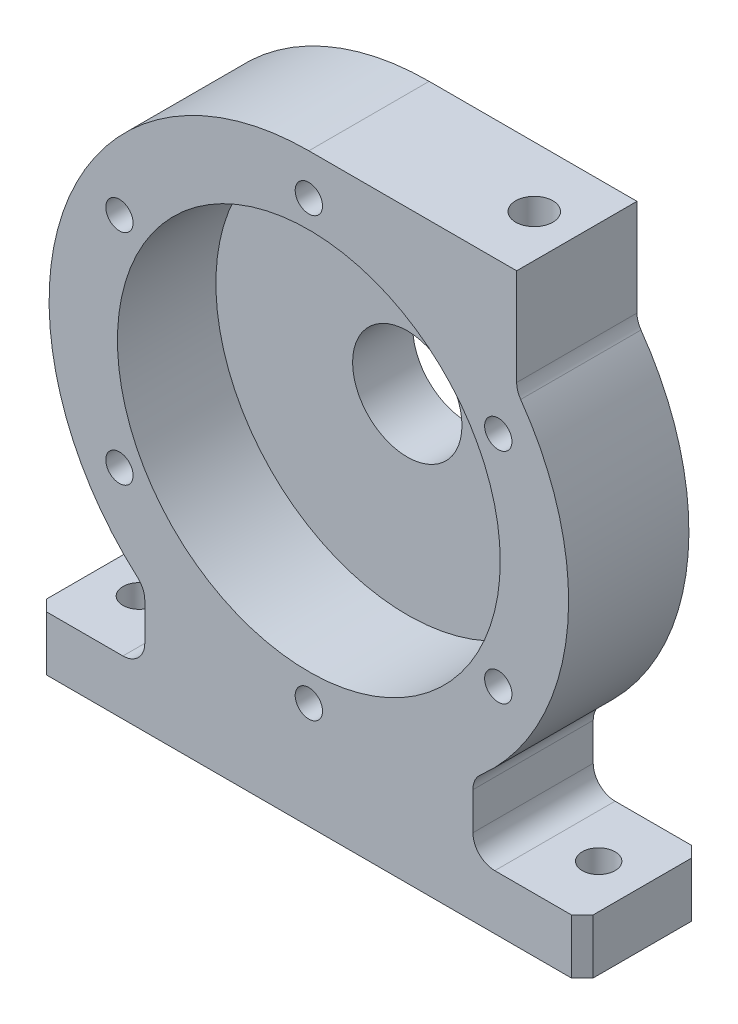
SolidWorks part; units mm, degrees
ref_plane "Front Plane" through (0, 0, 0) normal (0, 0, 1) x (1, 0, 0)
ref_plane "Top Plane" through (0, 0, 0) normal (0, 1, 0) x (1, 0, 0)
ref_plane "Right Plane" through (0, 0, 0) normal (1, 0, 0) x (0, 0, -1)
sketch "Sketch2" plane through (0, 0, 0) normal (0, 0, 1) x (1, 0, 0)
  line L0 (0, 0) -> (0, -59.5) construction
  line L1 (-50, -59.5) -> (50, -59.5)
  line L2 (50, -59.5) -> (50, -49.5)
  line L3 (50, -49.5) -> (34, -49.5)
  line L4 (30, -45.5) -> (30, -38.6814)
  line L5 (0, 47.5) -> (38, 47.5)
  line L6 (38, 47.5) -> (38, 29.8035)
  line L7 (-30, -45.5) -> (-30, -38.6814)
  line L8 (-50, -59.5) -> (-50, -49.5)
  line L9 (-50, -49.5) -> (-34, -49.5)
  arc A0 (0, 47.5) -> (-31.3592, -35.677) centre (0, 0) ccw
  arc A1 (31.3592, -35.677) -> (38.7379, 27.4887) centre (0, 0) ccw
  arc A2 (34, -49.5) -> (30, -45.5) centre (34, -45.5) cw
  arc A3 (30, -38.6814) -> (31.3592, -35.677) centre (34, -38.6814) cw
  arc A4 (38, 29.8035) -> (38.7379, 27.4887) centre (42, 29.8035) ccw
  arc A5 (-34, -49.5) -> (-30, -45.5) centre (-34, -45.5) ccw
  arc A6 (-30, -38.6814) -> (-31.3592, -35.677) centre (-34, -38.6814) ccw
  point P15 (30, -36.8273)
  point P18 (-30, -36.8273)
  dimension "D1" = 59.5
  dimension "D3" = 95
  dimension "D6" = 4
  dimension "D2" = 30
  dimension "D4" = 10
  dimension "D5" = 38
extrude "Boss-Extrude1" add sketch "Sketch2" along normal blind 22
sketch "Sketch3" plane through (0, 0, 22) normal (0, 0, 1) x (1, 0, 0)
  circle A0 centre (0, 0) radius 35
extrude "Cut-Extrude1" cut sketch "Sketch3" against normal blind 18
sketch "Sketch4" plane through (0, 0, 0) normal (0, 0, -1) x (-1, 0, 0)
  circle A0 centre (0, 0) radius 14
extrude "Boss-Extrude2" add sketch "Sketch4" along normal blind 7 contours A0
fillet "Fillet1" radius 4 1 edges at (-14, 0, 0)
sketch "Sketch5" plane through (0, 0, -7) normal (0, 0, -1) x (-1, 0, 0)
  circle A0 centre (0, 0) radius 10
extrude "Cut-Extrude2" cut sketch "Sketch5" against normal through all
chamfer "Chamfer1" distance 2 angle 45 4 edges at (50, -54.5, 0) (50, -54.5, 22) (-50, -54.5, 22) (-50, -54.5, 0)
sketch "Sketch6" plane through (0, 47.5, 0) normal (0, 1, 0) x (1, 0, 0)
  line L0 (0, -11) -> (38, -11) construction
  line L1 (0, -22) -> (0, 0) construction
  line L2 (38, -22) -> (38, 0) construction
hole_wizard "M8x1.25 Tapped Hole1" positions "3DSketch1" profile "Sketch7" tap size "M8x1.25" standard "ANSI Metric"
sketch3d "3DSketch1"
  line L0 (0, 47.5, 11) -> (38, 47.5, 11) construction
  point P0 (30.2242, 47.5, 11)
  dimension "D1" = 7.7759
sketch "Sketch7" plane through (30.2242, 47.5, 11) normal (1, 0, 0) x (0, 0, 1)
  line L0 (0, 0) -> (0, 31.7929)
  line L1 (0, 31.7929) -> (3.4, 29.75)
  line L2 (3.4, 29.75) -> (3.4, 0)
  line L5 (3.4, 0) -> (0, 0)
  line L10 (0, 31.7929) -> (-3.4, 29.75) construction
  line L11 (0, -6.35) -> (0, 107.95) construction
  dimension "Tap Drill Dia." = 6.8
  dimension "Tap Drill Depth" = 29.75
  dimension "Drill Angle" = 118
cosmetic thread "Hole Thread1" parameters "D1"=16, "D2"=8
sketch "Sketch8" plane through (0, 0, 22) normal (0, 0, 1) x (1, 0, 0)
  circle A0 centre (0, 0) radius 40 construction
hole_wizard "M6x1.0 Tapped Hole1" positions "Sketch10" profile "Sketch11" tap size "M6x1.0" standard "ANSI Metric"
sketch "Sketch10" plane through (0, 0, 22) normal (0, 0, 1) x (1, 0, 0)
  circle A0 centre (0, 0) radius 40 construction
  point P0 (0, 40)
sketch "Sketch11" plane through (0, 40, 22) normal (1, 0, 0) x (0, -1, 0)
  line L0 (0, 0) -> (0, 16.5022)
  line L1 (0, 16.5022) -> (2.5, 15)
  line L2 (2.5, 15) -> (2.5, 0)
  line L5 (2.5, 0) -> (0, 0)
  line L10 (0, 16.5022) -> (-2.5, 15) construction
  line L11 (0, -6.35) -> (0, 107.95) construction
  dimension "Tap Drill Dia." = 5
  dimension "Tap Drill Depth" = 15
  dimension "Drill Angle" = 118
cosmetic thread "Hole Thread2" parameters "D1"=12, "D2"=6
pattern_circular "CirPattern1" count 6 over 360 about axis through (0, 0, 0) along (0, 0, 1) of "M6x1.0 Tapped Hole1"
cosmetic thread "Hole Thread3" parameters "D1"=12, "D2"=6
cosmetic thread "Hole Thread4" parameters "D1"=12, "D2"=6
cosmetic thread "Hole Thread5" parameters "D1"=12, "D2"=6
cosmetic thread "Hole Thread6" parameters "D1"=12, "D2"=6
cosmetic thread "Hole Thread7" parameters "D1"=12, "D2"=6
hole_wizard "CSK for M6 Countersunk Flat Head Screw2" positions "Sketch16" profile "Sketch17" countersink size "M6" standard "ISO"
sketch "Sketch16" plane through (0, -59.5, 0) normal (0, -1, 0) x (-1, 0, 0)
  line L0 (50, -20) -> (50, -2) construction
  line L1 (-50, -20) -> (-50, -2) construction
  point P0 (-42, -11)
  point P2 (42, -11)
  dimension "D1" = 8
  dimension "D2" = 8
sketch "Sketch17" plane through (42, -59.5, 11) normal (1, 0, 0) x (0, 0, -1)
  line L0 (0, 0) -> (0, 21.8026)
  line L1 (0, 21.8026) -> (3, 20)
  line L2 (3, 20) -> (3, 1)
  line L3 (3, 1) -> (4, 0)
  line L5 (4, 0) -> (0, 0)
  line L6 (-3, 1) -> (-4, 0) construction
  line L10 (0, 21.8026) -> (-3, 20) construction
  line L11 (0, -6.35) -> (0, 107.95) construction
  dimension "Hole Dia." = 6
  dimension "Hole Depth" = 20
  dimension "Near C'Sink Dia." = 8
  dimension "Near C'Sink Angle" = 90
  dimension "Drill Angle" = 118
